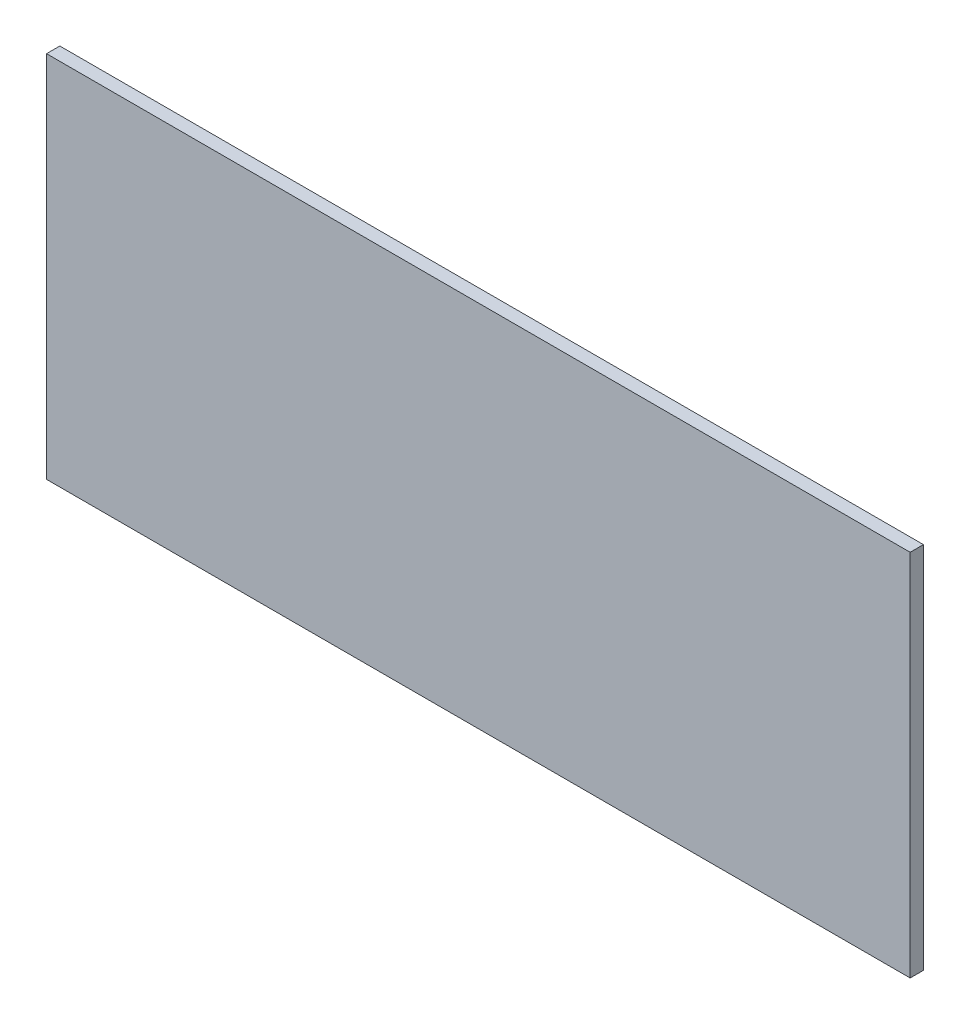
SolidWorks part; units mm, degrees
ref_plane "Alzado" through (0, 0, 0) normal (0, 0, 1) x (1, 0, 0)
ref_plane "Planta" through (0, 0, 0) normal (0, 1, 0) x (1, 0, 0)
ref_plane "Vista lateral" through (0, 0, 0) normal (1, 0, 0) x (0, 0, -1)
sketch "Croquis1" plane through (0, 0, 0) normal (0, 0, 1) x (1, 0, 0)
  line L1 (-604.9551, 210.2941) -> (695.0449, 210.2941)
  line L2 (-604.9551, 210.2941) -> (-604.9551, -344.7059)
  line L3 (-604.9551, -344.7059) -> (695.0449, -344.7059)
  line L4 (695.0449, 210.2941) -> (695.0449, -344.7059)
  dimension "D1" = 1300
  dimension "D2" = 555
extrude "Saliente-Extruir1" add sketch "Croquis1" along normal blind 20
